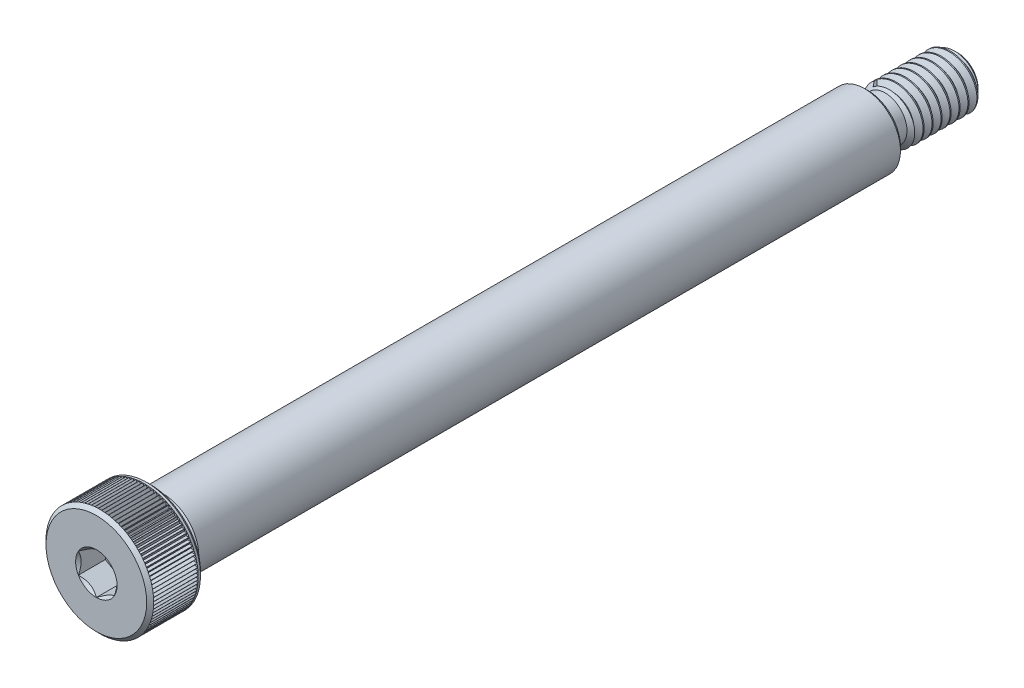
SolidWorks part; units mm, degrees
material "1.4310 (X10CrNi18-8)"
ref_plane "Front Plane" through (0, 0, 0) normal (0, 0, 1) x (1, 0, 0)
ref_plane "Top Plane" through (0, 0, 0) normal (0, 1, 0) x (1, 0, 0)
ref_plane "Right Plane" through (0, 0, 0) normal (1, 0, 0) x (0, 0, -1)
sketch "Sketch1" plane through (0, 0, 0) normal (1, 0, 0) x (0, 0, -1)
  line L0 (-24, 0) -> (24, 0) construction
  line L1 (-24, -3) -> (-24, 3) construction
  line L2 (-24, 3) -> (-21, 3) construction
  line L3 (-21, 3) -> (-21, 1.797) construction
  line L4 (-21, 1.797) -> (-20.492, 1.797) construction
  line L5 (-20.492, 1.797) -> (-20.289, 2) construction
  line L6 (-20.289, 2) -> (19, 2) construction
  line L7 (23.9688, 1.5541) -> (24.2188, 1.1211) construction
  line L8 (24.2188, 1.1211) -> (24.4688, 1.5541) construction
  line L9 (24, -1.5) -> (24, 1.5) construction
  line L10 (19, 2) -> (24, 2) construction
  line L11 (24.4688, 1.5541) -> (23.9688, 1.5541) construction
  line L12 (24.2188, 1.5541) -> (24.2188, 1.5) construction
  line L13 (24.2188, 1.1211) -> (24.2188, 1.1752) construction
  line L14 (24.25, 1.1752) -> (24.1875, 1.1752) construction
  line L15 (24.4375, 1.5) -> (24, 1.5) construction
  line L16 (24.2188, 1.5271) -> (24.4531, 1.5271) construction
  line L17 (24.2188, 1.5271) -> (23.9844, 1.5271) construction
  line L18 (-24, 2.805) -> (-23.805, 3) construction
  line L19 (-21.195, 3) -> (-21, 2.805) construction
  line L20 (24, 1.5) -> (19, 1.5) construction
  line L21 (23.625, 1.5) -> (24, 1.125) construction
  line L22 (20.2313, 1.5) -> (19.95, 1.2188) construction
  line L23 (19.95, 1.2188) -> (19.1406, 1.2187) construction
  line L24 (19, 1.5) -> (19, 1.3594) construction
  line L25 (-22.5, 1) -> (-22.5, -1) construction
  line L26 (-22.5, -1) -> (-24, -1) construction
  line L27 (-22.5, 1) -> (-24, 1) construction
  line L28 (-23.805, 0) -> (-21.3255, 0) construction
  arc A0 (19, 1.3594) -> (19.1406, 1.2187) centre (19.1406, 1.3594) ccw construction
  point P4 (0, 0)
  point P7 (-24, 0)
  point P18 (24, 0)
  point P25 (22.25, -1.5)
  point P38 (-22.5, 3)
  point P45 (-22.5, 0)
  point P46 (20.0906, 1.3594)
  point P48 (-20.492, 0)
  point P51 (-22.5, 0)
  point P52 (19, 0)
  point P53 (-19.2, 0)
  dimension "Head Diameter" = 6
  dimension "Head Height" = 3
  dimension "Thread Diameter" = 3
  dimension "Shoulder Diameter" = 4
  dimension "Thread Length" = 5
  dimension "D1" = 0.508
  dimension "D2" = 135
  dimension "D3" = 0.203
  dimension "Shoulder Length" = 40
  dimension "Thread Pitch" = 0.5
  dimension "D4" = 0.0625
  dimension "D5" = 1.75
  dimension "D6" = 0.195
  dimension "D7" = 0.375
  dimension "D8" = 2.4375
  dimension "D9" = 0.95
  dimension "Drive Size" = 2
  dimension "Knurling Length" = 2.4795
  dimension "D10" = 4.8
sketch "Sketch3" plane through (0, 0, 0) normal (1, 0, 0) x (0, 0, -1)
  line L0 (-24, 0) -> (-24, 2.805)
  line L1 (-24, -3) -> (-24, 3) construction
  line L2 (-24, 2.805) -> (-23.805, 3)
  line L3 (-23.805, 3) -> (-21.195, 3)
  line L4 (-21.195, 3) -> (-21, 2.805)
  line L5 (-21, 2.805) -> (-21, 1.797)
  line L6 (-21, 1.797) -> (-20.492, 1.797)
  line L7 (-20.492, 1.797) -> (-20.289, 2)
  line L8 (-20.289, 2) -> (19, 2)
  line L9 (19, 2) -> (19, 1.3594)
  line L10 (19.1406, 1.2187) -> (19.95, 1.2188)
  line L11 (19.95, 1.2188) -> (20.2313, 1.5)
  line L12 (20.2313, 1.5) -> (23.625, 1.5)
  line L13 (23.625, 1.5) -> (24, 1.125)
  line L14 (24, 1.125) -> (24, 0)
  line L15 (24, 0) -> (-24, 0)
  arc A0 (19, 1.3594) -> (19.1406, 1.2187) centre (19.1406, 1.3594) ccw construction
  arc A1 (19, 1.3594) -> (19.1406, 1.2187) centre (19.1406, 1.3594) ccw
revolve "Revolve1" add sketch "Sketch3" angle 360 about L0
sketch "Sketch4" plane through (0, 0, 0) normal (0, 0, 1) x (1, 0, 0)
  line L0 (0, -3) -> (0, 3) construction
  line L1 (0, 1.1547) -> (-1, 0.5774)
  line L2 (-1, 0.5774) -> (-1, -0.5774)
  line L3 (-1, -0.5774) -> (0, -1.1547)
  line L4 (0, -1.1547) -> (1, -0.5774)
  line L5 (1, -0.5774) -> (1, 0.5774)
  line L6 (1, 0.5774) -> (0, 1.1547)
  circle A0 centre (0, 0) radius 1 construction
extrude "Cut-Extrude1" cut sketch "Sketch4" against normal up to vertex (-22.5 mm away) from vertex at 24 starting at point (0, 0, 24)
sketch "Sketch5" plane through (0, 0, 0) normal (0, 0, 1) x (1, 0, 0)
  line L0 (0, -3) -> (0, 3) construction
  circle A0 centre (0, 0) radius 1.1547
extrude "Cut-Extrude2" cut sketch "Sketch5" against normal up to vertex (-22.5 mm away) draft 45 from vertex at 24 starting at point (0, 0, 24)
chamfer "Chamfer1" distance 0.195 angle 45 1 edges at (2, 0, -19)
sketch "Sketch6" plane through (0, 0, -24) normal (0, 0, -1) x (-1, 0, 0)
  circle A0 centre (0, 0) radius 1.5
curve "Helix/Spiral1" pitch 0.5 height 4.05 turns 8.1
sketch "Sketch7" plane through (0, 0, 0) normal (1, 0, 0) x (0, 0, -1)
  line L0 (23.9844, 1.5271) -> (24.1875, 1.1752)
  line L1 (24.1875, 1.1752) -> (24.25, 1.1752)
  line L2 (24.25, 1.1752) -> (24.4531, 1.5271)
  line L3 (24.4531, 1.5271) -> (23.9844, 1.5271)
sweep "Cut-Sweep1" cut profiles "Sketch7" path "Helix/Spiral1"
sketch "Sketch8" plane through (0, 0, 0) normal (0, 0, 1) x (1, 0, 0)
  line L0 (0, 3) -> (0, 0) construction
  line L1 (-0.0901, 3) -> (0.0901, 3)
  line L2 (0.0901, 3) -> (0, 2.844)
  line L3 (0, 2.844) -> (-0.0901, 3)
  line L4 (-0.0901, 3) -> (0, 0) construction
  line L5 (0, 0) -> (0.0901, 3) construction
  circle A0 centre (0, 0) radius 2.844 construction
  point P8 (0, 3)
  dimension "D1" = 0.156
  dimension "D2" = 3.439
extrude "Cut-Extrude3" cut sketch "Sketch8" against normal up to vertex (-21.3255 mm away) from vertex at 23.805 starting at point (0, 0, 23.805)
pattern_circular "CirPattern1" count 99 over 360 about axis through (0, 0, 0) along (0, 0, 1) of "Cut-Extrude3"
equation "\"D4@Sketch1\"=\"Thread Pitch@Sketch1\"/8"
equation "\"D5@Sketch1\"=\"Thread Pitch@Sketch1\"*3.5"
equation "\"D6@Sketch1\"=\"Head Diameter@Sketch1\"*.0325"
equation "\"D7@Sketch1\"=\"Thread Pitch@Sketch1\"*.75"
equation "\"D1@Chamfer1\"=\"D6@Sketch1\""
equation "\"D4@Helix/Spiral1\"=\"Thread Pitch@Sketch1\""
equation "\"D3@Helix/Spiral1\" = \"Thread Length@Sketch1\" - \"D9@Sketch1\""
equation "\"D1@Sketch8\"=\"D6@Sketch1\"*.8"
equation "\"D1@CirPattern1\"=(360/\"D2@Sketch8\")-6"
equation "\"D9@Sketch1\"  = \"Thread Length@Sketch1\"*.2"
equation "\"D8@Sketch1\"=\"Thread Diameter@Sketch1\"*.65"
equation "\"D10@Sketch1\"=\"Head Diameter@Sketch1\"*.8"
